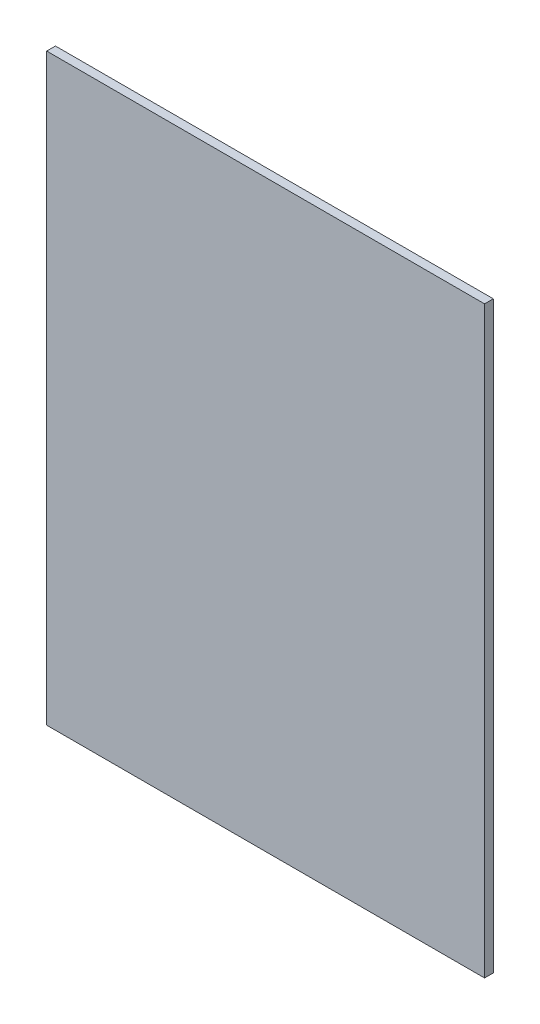
SolidWorks part; units mm, degrees
material "C-Fibra di vetro"
ref_plane "Piano frontale" through (0, 0, 0) normal (0, 0, 1) x (1, 0, 0)
ref_plane "Piano superiore" through (0, 0, 0) normal (0, 1, 0) x (1, 0, 0)
ref_plane "Piano destro" through (0, 0, 0) normal (1, 0, 0) x (0, 0, -1)
sketch "Schizzo1" plane through (0, 0, 0) normal (0, 0, 1) x (1, 0, 0)
  line L1 (-75, 100) -> (75, 100)
  line L2 (-75, 100) -> (-75, -100)
  line L3 (-75, -100) -> (75, -100)
  line L4 (75, 100) -> (75, -100)
  line L5 (-75, 100) -> (75, -100) construction
  line L6 (-75, -100) -> (75, 100) construction
  point P0 (0, 0)
  dimension "D1" = 150
  dimension "D2" = 200
extrude "Estrusione-Estrusione1" add sketch "Schizzo1" along normal blind 3
